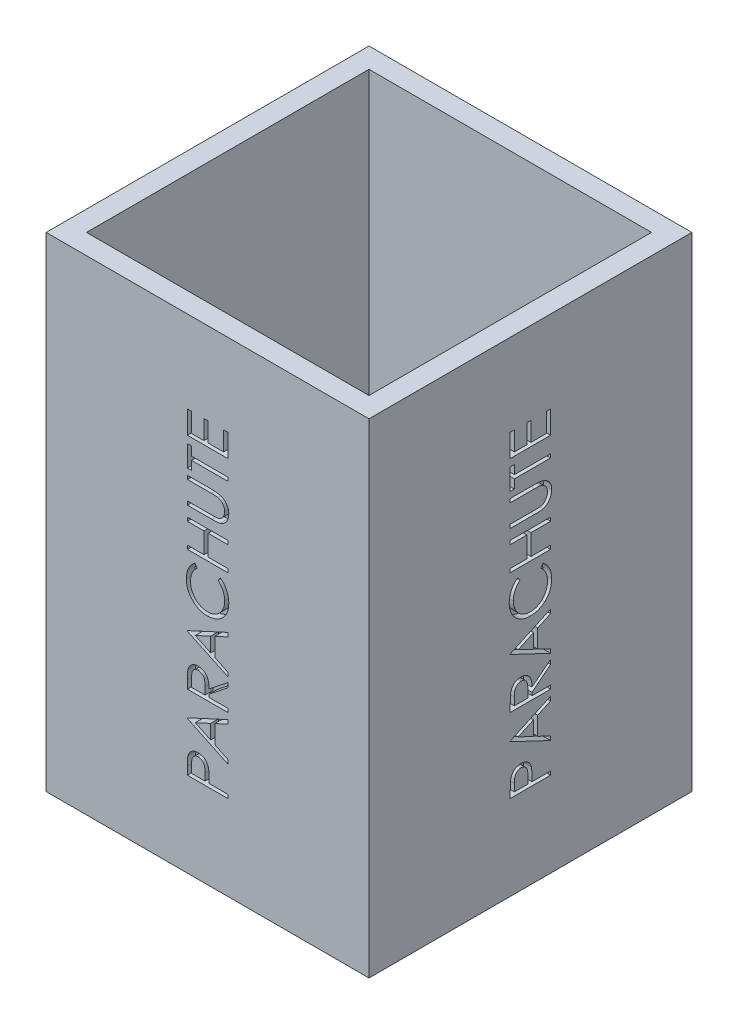
SolidWorks part; units mm, degrees
material "PVC Rigid"
ref_plane "Front Plane" through (0, 0, 0) normal (0, 0, 1) x (1, 0, 0)
ref_plane "Top Plane" through (0, 0, 0) normal (0, 1, 0) x (1, 0, 0)
ref_plane "Right Plane" through (0, 0, 0) normal (1, 0, 0) x (0, 0, -1)
sketch "Sketch1" plane through (0, 0, 0) normal (0, 1, 0) x (1, 0, 0)
  line L1 (-50.8, -50.8) -> (50.8, -50.8)
  line L2 (-50.8, -50.8) -> (-50.8, 50.8)
  line L3 (-50.8, 50.8) -> (50.8, 50.8)
  line L4 (50.8, -50.8) -> (50.8, 50.8)
  line L5 (-50.8, -50.8) -> (50.8, 50.8) construction
  line L6 (-50.8, 50.8) -> (50.8, -50.8) construction
  line L7 (-44.45, -44.45) -> (44.45, -44.45)
  line L8 (-44.45, -44.45) -> (-44.45, 44.45)
  line L9 (-44.45, 44.45) -> (44.45, 44.45)
  line L10 (44.45, -44.45) -> (44.45, 44.45)
  line L11 (-44.45, -44.45) -> (44.45, 44.45) construction
  line L12 (-44.45, 44.45) -> (44.45, -44.45) construction
  point P0 (0, 0)
  point P6 (0, 0)
  dimension "D1" = 101.6
  dimension "D2" = 101.6
  dimension "D3" = 88.9
extrude "Boss-Extrude1" add sketch "Sketch1" along normal blind 152.4
sketch "Sketch6" plane through (-50.8, 0, 0) normal (-1, 0, 0) x (0, 0, 1)
  line L0 (6.35, 0) -> (6.35, 152.4) construction
  line L1 (-50.8, 0) -> (50.8, 0) construction
  line L2 (-50.8, 152.4) -> (50.8, 152.4) construction
  line L3 (-50.8, 152.4) -> (-50.8, 0) construction
  text T0 "PARACHUTE" font "Century Gothic" height in points 48
  dimension "D1" = 57.15
extrude "Cut-Extrude1" cut sketch "Sketch6" against normal blind 2.54
sketch "Sketch7" plane through (0, 0, 0) normal (0, 0, 1) x (1, 0, 0)
  line L0 (0, 0) -> (0, 152.4) construction
  line L1 (-50.8, 152.4) -> (50.8, 152.4) construction
pattern_circular "CirPattern1" count 4 over 360 about axis through (0, 0, 0) along (0, 1, 0) of "Cut-Extrude1"
